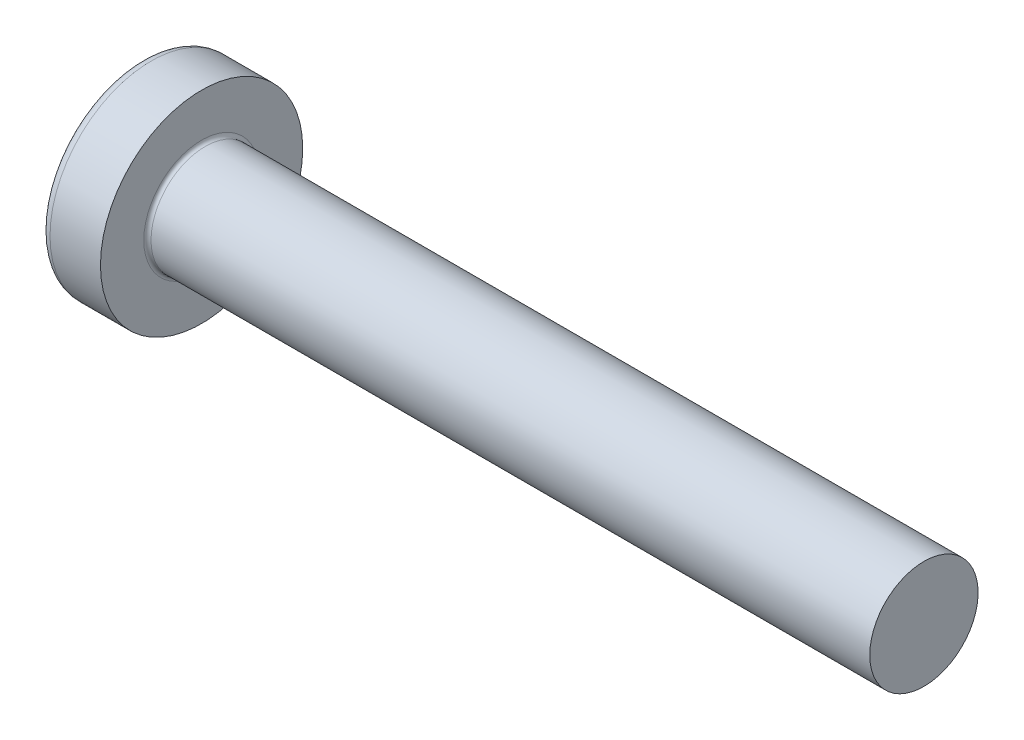
SolidWorks part; units mm, degrees
ref_plane "Plane1" through (0, 0, 0) normal (0, 0, 1) x (1, 0, 0)
ref_plane "Plane2" through (0, 0, 0) normal (0, 1, 0) x (1, 0, 0)
ref_plane "Plane3" through (0, 0, 0) normal (1, 0, 0) x (0, 0, -1)
sketch "BodySke" plane through (0, 0, 0) normal (0, 0, 1) x (1, 0, 0)
  line L0 (2.4, 1.5) -> (2.4, 2.8)
  line L1 (2.65, 6.35) -> (2.65, -3.175) construction
  line L2 (-25.4, 0) -> (127, 0) construction
  line L3 (22.4, 0) -> (0, 0)
  line L4 (2.4, 1.5) -> (22.4, 1.5)
  line L5 (22.4, 1.5) -> (22.4, 0)
  line L6 (1.0035, 2.8) -> (2.4, 2.8)
  line L8 (2.4, 6.35) -> (2.4, -3.175) construction
  arc A0 (0.7754, 2.6744) -> (0, 0) centre (5, 0) ccw
  arc A2 (0.7754, 2.6744) -> (1.0035, 2.8) centre (1.0035, 2.53) cw
  dimension "Head_fillet_rad" = 0.27
  dimension "Head_crown_rad" = 5
  dimension "Head_ht" = 2.4
  dimension "Diameter" = 3
  dimension "Length" = 20
  dimension "Head_dia" = 5.6
  dimension "Advance" = 0.5
  dimension "Thread_nom" = 20
revolve "Base-Revolve" add sketch "BodySke"
cosmetic thread "ThreadCosmetic" [suppressed]
fillet "Fillet1" radius 0.1 1 edges at (2.4, 0, 1.5)
sketch "Sketch3" plane through (0, 0, 0) normal (1, 0, 0) x (0, 0, -1)
  line L0 (0.37, -1.4) -> (-0.37, -1.4)
  line L1 (0.37, -1.4) -> (0.37, 1.4)
  line L2 (-0.37, 1.4) -> (0.37, 1.4)
  line L3 (-0.37, 1.4) -> (-0.37, -1.4)
  dimension "D1" = 1.4
  dimension "Cross_dia" = 2.8
  dimension "D2" = 0.37
  dimension "Cross_width" = 0.74
ref_plane "Plane4" through (1.75, 0, 0) normal (1, 0, 0) x (0, 0, -1)
sketch "Sketch4" plane through (1.75, 0, 0) normal (1, 0, 0) x (0, 0, -1)
  line L0 (0.37, -0.5275) -> (-0.37, -0.5275)
  line L1 (0.37, -0.5275) -> (0.37, 0.5275)
  line L2 (-0.37, 0.5275) -> (0.37, 0.5275)
  line L3 (-0.37, 0.5275) -> (-0.37, -0.5275)
  dimension "D1" = 0.74
  dimension "D2" = 1.055
  dimension "D3" = 0.37
  dimension "D4" = 0.5275
loft "Recess" cut profiles "Sketch3", "Sketch4"
pattern_circular "RecPat" count 2 every 90 about axis through (0, 0, 0) along (1, 0, 0) of "Recess"
sketch "RecCorSke" plane through (0, 0, 0) normal (0, 0, 1) x (1, 0, 0)
  line L0 (-3.175, 0) -> (15.875, 0) construction
  line L1 (-25.4, 0) -> (127, 0) construction
  line L2 (0, 0) -> (0, 0.6784)
  line L3 (0, 0.6784) -> (1.75, 0.556)
  line L4 (1.75, 0.556) -> (1.9307, 0)
  line L5 (1.9307, 0) -> (0, 0)
  dimension "Diameter" = 1.112
  dimension "Depth" = 1.75
  dimension "Draft_angle" = 4
  dimension "Bottom_angle" = 18
revolve "RecessCore" cut sketch "RecCorSke" angle 360 about L0
sketch "ThdSchSke" plane through (0, 0, 0) normal (0, 0, 1) x (1, 0, 0)
  line L0 (3.4, -1.2195) -> (3.2036, -1.5)
  line L1 (3.4, -1.2195) -> (3.5964, -1.5)
  line L2 (3.5964, -1.5) -> (3.5964, -1.875)
  line L3 (-3.175, 0) -> (5.1513, 0) construction
  line L5 (3.5964, -1.875) -> (3.2036, -1.875)
  line L6 (3.2036, -1.875) -> (3.2036, -1.5)
  dimension "Thread_minor" = 2.439
  dimension "Diameter" = 3
  dimension "Start" = 3.4
  dimension "SideAngle" = 55
  dimension "VeeAngle" = 70
  dimension "Overcut" = 3.75
revolve "ThreadSchematic" [suppressed] cut sketch "ThdSchSke" angle 360 about L3
pattern_linear "ThdSchPat" [suppressed]
equation "\"D1@Sketch3\" = \"Cross_dia@Sketch3\" / 2"
equation "\"D2@Sketch3\" = \"Cross_width@Sketch3\" / 2"
equation "\"Depth@RecCorSke\" = \"Cross_depth@Plane4\""
equation "\"D1@Sketch4\" = \"Cross_width@Sketch3\""
equation "\"D2@Sketch4\" = \"Cross_dia@Sketch3\" - 2.0 * \"Cross_depth@Plane4\" * tan(26.5  * 0.017453292)"
equation "\"D3@Sketch4\" = \"D1@Sketch4\" / 2"
equation "\"D4@Sketch4\" = \"D2@Sketch4\" / 2"
equation "\"Thread_length@ThreadCosmetic\" = ((sgn( (\"Length@BodySke\" - \"Advance@BodySke\" * 2.0 ) - \"Thread_nom@BodySke\" )-1)*( (\"Length@BodySke\" - \"Advance@BodySke\" * 2.0 ) - \"Thread_nom@BodySke\" ))/-2+ \"Thread_nom@BodySke\""
equation "\"Thread_minor@ThdSchSke\" = \"Thread_minor@ThreadCosmetic\""
equation "\"Diameter@ThdSchSke\" = \"Diameter@BodySke\""
equation "\"Overcut@ThdSchSke\" = \"Diameter@BodySke\" * 1.25"
equation "\"Start@ThdSchSke\" = \"Head_ht@BodySke\" + \"Length@BodySke\" - \"Thread_length@ThreadCosmetic\"  '---Non-countersunk---"
equation "\"Num_threads@ThdSchPat\" = int( \"Thread_length@ThreadCosmetic\" / \"Advance@BodySke\" + 0.999 )  + 1"
equation "\"Advance@ThdSchPat\" = \"Thread_length@ThreadCosmetic\" /  (\"Num_threads@ThdSchPat\" - 1) 'relax it"
